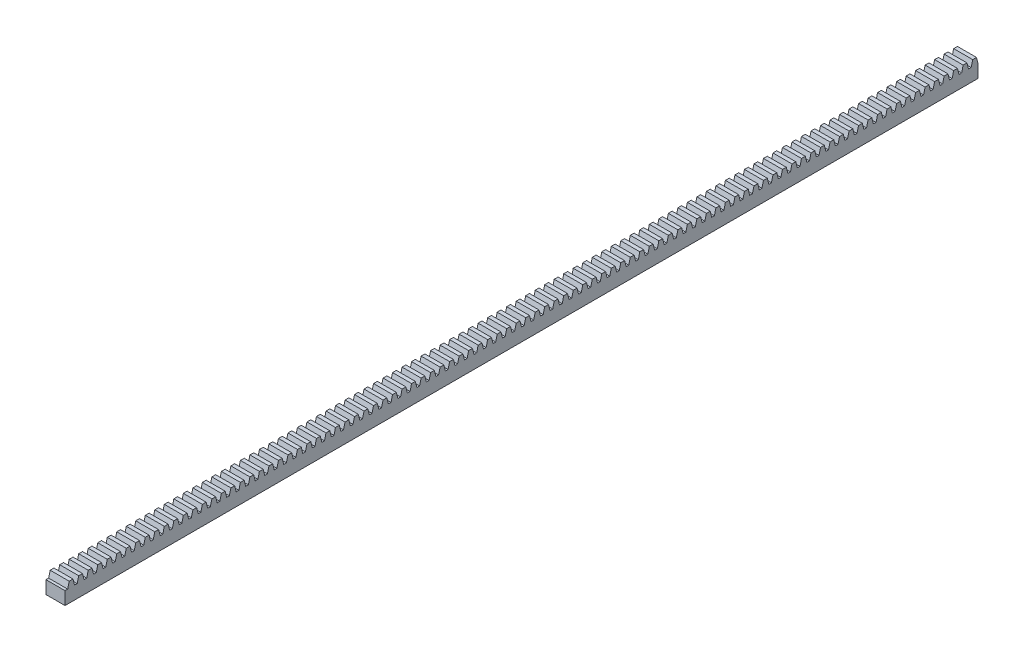
SolidWorks part; units mm, degrees
ref_plane "Front Plane" through (0, 0, 0) normal (0, 0, 1) x (1, 0, 0)
ref_plane "Top Plane" through (0, 0, 0) normal (0, 1, 0) x (1, 0, 0)
ref_plane "Right Plane" through (0, 0, 0) normal (1, 0, 0) x (0, 0, -1)
sketch "Sketch1" plane through (0, 0, 0) normal (0, 0, 1) x (1, 0, 0)
  line L1 (0, 0) -> (6.35, 0)
  line L2 (0, 0) -> (0, 4.318)
  line L3 (0, 4.318) -> (6.35, 4.318)
  line L4 (6.35, 0) -> (6.35, 4.318)
  dimension "D1" = 6.35
  dimension "D2" = 4.318
extrude "Boss-Extrude1" add sketch "Sketch1" along normal blind 304.8
sketch "Sketch2" plane through (6.35, 0, 0) normal (1, 0, 0) x (0, 0, -1)
  line L0 (0, 4.318) -> (-2.286, 4.318)
  line L1 (-304.8, 4.318) -> (0, 4.318) construction
  line L2 (-1.778, 6.35) -> (-0.508, 6.35)
  line L3 (-1.778, 6.35) -> (-2.286, 4.318)
  line L4 (-0.508, 6.35) -> (0, 4.318)
  line L5 (-304.8, 0) -> (0, 0) construction
  dimension "D1" = 2.286
  dimension "D2" = 1.27
  dimension "D3" = 6.35
extrude "Boss-Extrude2" add sketch "Sketch2" against normal blind 6.35
pattern_linear "LPattern1" count 96 spacing 3.175 along (0, 0, 1) of "Boss-Extrude2"
